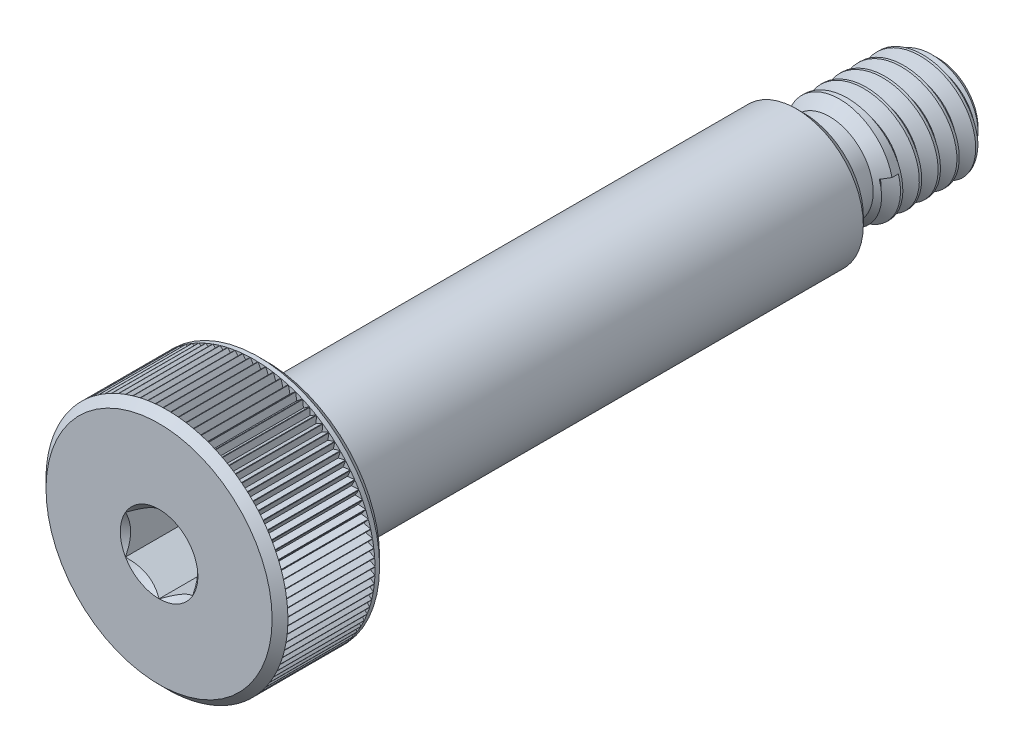
SolidWorks part; units mm, degrees
ref_plane "Front Plane" through (0, 0, 0) normal (0, 0, 1) x (1, 0, 0)
ref_plane "Top Plane" through (0, 0, 0) normal (0, 1, 0) x (1, 0, 0)
ref_plane "Right Plane" through (0, 0, 0) normal (1, 0, 0) x (0, 0, -1)
sketch "Sketch1" plane through (0, 0, 0) normal (1, 0, 0) x (0, 0, -1)
  line L0 (-14.5, 0) -> (14.5, 0) construction
  line L1 (-14.5, -4.5) -> (-14.5, 4.5) construction
  line L2 (-14.5, 4.5) -> (-10.5, 4.5) construction
  line L3 (-10.5, 4.5) -> (-10.5, 2.297) construction
  line L4 (-10.5, 2.297) -> (-9.992, 2.297) construction
  line L5 (-9.992, 2.297) -> (-9.789, 2.5) construction
  line L6 (-9.789, 2.5) -> (9.5, 2.5) construction
  line L7 (14.4563, 2.0758) -> (14.8063, 1.4696) construction
  line L8 (14.8063, 1.4696) -> (15.1563, 2.0758) construction
  line L9 (14.5, -2) -> (14.5, 2) construction
  line L10 (9.5, 2.5) -> (14.5, 2.5) construction
  line L11 (15.1563, 2.0758) -> (14.4563, 2.0758) construction
  line L12 (14.8063, 2.0758) -> (14.8063, 2) construction
  line L13 (14.8063, 1.4696) -> (14.8063, 1.5453) construction
  line L14 (14.85, 1.5453) -> (14.7625, 1.5453) construction
  line L15 (15.1125, 2) -> (14.5, 2) construction
  line L16 (14.8063, 2.0379) -> (15.1344, 2.0379) construction
  line L17 (14.8063, 2.0379) -> (14.4781, 2.0379) construction
  line L18 (-14.5, 4.2075) -> (-14.2075, 4.5) construction
  line L19 (-10.7925, 4.5) -> (-10.5, 4.2075) construction
  line L20 (14.5, 2) -> (9.5, 2) construction
  line L21 (13.975, 2) -> (14.5, 1.475) construction
  line L22 (10.825, 2) -> (10.45, 1.625) construction
  line L23 (10.45, 1.625) -> (9.6875, 1.625) construction
  line L24 (9.5, 2) -> (9.5, 1.8125) construction
  line L25 (-12.5, 1.25) -> (-12.5, -1.25) construction
  line L26 (-12.5, -1.25) -> (-14.5, -1.25) construction
  line L27 (-12.5, 1.25) -> (-14.5, 1.25) construction
  line L28 (-14.2075, 0) -> (-10.9633, 0) construction
  arc A0 (9.5, 1.8125) -> (9.6875, 1.625) centre (9.6875, 1.8125) ccw construction
  point P4 (0, 0)
  point P7 (-14.5, 0)
  point P18 (14.5, 0)
  point P25 (12.05, -2)
  point P38 (-12.5, 4.5)
  point P45 (-12.5, 0)
  point P46 (10.6375, 1.8125)
  point P48 (-9.992, 0)
  point P51 (-12.5, 0)
  point P52 (9.5, 0)
  point P53 (-7.3, 0)
  dimension "Head Diameter" = 9
  dimension "Head Height" = 4
  dimension "Thread Diameter" = 4
  dimension "Shoulder Diameter" = 5
  dimension "Thread Length" = 5
  dimension "D1" = 0.508
  dimension "D2" = 135
  dimension "D3" = 0.203
  dimension "Shoulder Length" = 20
  dimension "Thread Pitch" = 0.7
  dimension "D4" = 0.0875
  dimension "D5" = 2.45
  dimension "D6" = 0.2925
  dimension "D7" = 0.525
  dimension "D8" = 3.25
  dimension "D9" = 0.95
  dimension "Drive Size" = 2.5
  dimension "Knurling Length" = 3.2443
  dimension "D10" = 7.2
sketch "Sketch3" plane through (0, 0, 0) normal (1, 0, 0) x (0, 0, -1)
  line L0 (-14.5, 0) -> (-14.5, 4.2075)
  line L1 (-14.5, -4.5) -> (-14.5, 4.5) construction
  line L2 (-14.5, 4.2075) -> (-14.2075, 4.5)
  line L3 (-14.2075, 4.5) -> (-10.7925, 4.5)
  line L4 (-10.7925, 4.5) -> (-10.5, 4.2075)
  line L5 (-10.5, 4.2075) -> (-10.5, 2.297)
  line L6 (-10.5, 2.297) -> (-9.992, 2.297)
  line L7 (-9.992, 2.297) -> (-9.789, 2.5)
  line L8 (-9.789, 2.5) -> (9.5, 2.5)
  line L9 (9.5, 2.5) -> (9.5, 1.8125)
  line L10 (9.6875, 1.625) -> (10.45, 1.625)
  line L11 (10.45, 1.625) -> (10.825, 2)
  line L12 (10.825, 2) -> (13.975, 2)
  line L13 (13.975, 2) -> (14.5, 1.475)
  line L14 (14.5, 1.475) -> (14.5, 0)
  line L15 (14.5, 0) -> (-14.5, 0)
  arc A0 (9.5, 1.8125) -> (9.6875, 1.625) centre (9.6875, 1.8125) ccw construction
  arc A1 (9.5, 1.8125) -> (9.6875, 1.625) centre (9.6875, 1.8125) ccw
revolve "Revolve1" add sketch "Sketch3" angle 360 about L0
sketch "Sketch4" plane through (0, 0, 0) normal (0, 0, 1) x (1, 0, 0)
  line L0 (0, -4.5) -> (0, 4.5) construction
  line L1 (0, 1.4434) -> (-1.25, 0.7217)
  line L2 (-1.25, 0.7217) -> (-1.25, -0.7217)
  line L3 (-1.25, -0.7217) -> (0, -1.4434)
  line L4 (0, -1.4434) -> (1.25, -0.7217)
  line L5 (1.25, -0.7217) -> (1.25, 0.7217)
  line L6 (1.25, 0.7217) -> (0, 1.4434)
  circle A0 centre (0, 0) radius 1.25 construction
extrude "Cut-Extrude1" cut sketch "Sketch4" against normal up to vertex (-12.5 mm away) from vertex at 14.5 starting at point (0, 0, 14.5)
sketch "Sketch5" plane through (0, 0, 0) normal (0, 0, 1) x (1, 0, 0)
  line L0 (0, -4.5) -> (0, 4.5) construction
  circle A0 centre (0, 0) radius 1.4434
extrude "Cut-Extrude2" cut sketch "Sketch5" against normal up to vertex (-12.5 mm away) draft 45 from vertex at 14.5 starting at point (0, 0, 14.5)
chamfer "Chamfer1" distance 0.2925 angle 45 1 edges at (2.5, 0, -9.5)
sketch "Sketch6" plane through (0, 0, -14.5) normal (0, 0, -1) x (-1, 0, 0)
  circle A0 centre (0, 0) radius 2
curve "Helix/Spiral1" pitch 0.7 height 4.05 turns 5.7857
sketch "Sketch7" plane through (0, 0, 0) normal (1, 0, 0) x (0, 0, -1)
  line L0 (14.4781, 2.0379) -> (14.7625, 1.5453)
  line L1 (14.7625, 1.5453) -> (14.85, 1.5453)
  line L2 (14.85, 1.5453) -> (15.1344, 2.0379)
  line L3 (15.1344, 2.0379) -> (14.4781, 2.0379)
sweep "Cut-Sweep1" cut profiles "Sketch7" path "Helix/Spiral1"
sketch "Sketch8" plane through (0, 0, 0) normal (0, 0, 1) x (1, 0, 0)
  line L0 (0, 4.5) -> (0, 0) construction
  line L1 (-0.1351, 4.5) -> (0.1351, 4.5)
  line L2 (0.1351, 4.5) -> (0, 4.266)
  line L3 (0, 4.266) -> (-0.1351, 4.5)
  line L4 (-0.1351, 4.5) -> (0, 0) construction
  line L5 (0, 0) -> (0.1351, 4.5) construction
  circle A0 centre (0, 0) radius 4.266 construction
  point P8 (0, 4.5)
  dimension "D1" = 0.234
  dimension "D2" = 3.439
extrude "Cut-Extrude3" cut sketch "Sketch8" against normal up to vertex (-10.9633 mm away) from vertex at 14.2075 starting at point (0, 0, 14.2075)
pattern_circular "CirPattern1" count 99 over 360 about axis through (0, 0, 0) along (0, 0, 1) of "Cut-Extrude3"
equation "\"D4@Sketch1\"=\"Thread Pitch@Sketch1\"/8"
equation "\"D5@Sketch1\"=\"Thread Pitch@Sketch1\"*3.5"
equation "\"D6@Sketch1\"=\"Head Diameter@Sketch1\"*.0325"
equation "\"D7@Sketch1\"=\"Thread Pitch@Sketch1\"*.75"
equation "\"D1@Chamfer1\"=\"D6@Sketch1\""
equation "\"D4@Helix/Spiral1\"=\"Thread Pitch@Sketch1\""
equation "\"D3@Helix/Spiral1\" = \"Thread Length@Sketch1\" - \"D9@Sketch1\""
equation "\"D1@Sketch8\"=\"D6@Sketch1\"*.8"
equation "\"D1@CirPattern1\"=(360/\"D2@Sketch8\")-6"
equation "\"D9@Sketch1\"  = \"Thread Length@Sketch1\"*.2"
equation "\"D8@Sketch1\"=\"Thread Diameter@Sketch1\"*.65"
equation "\"D10@Sketch1\"=\"Head Diameter@Sketch1\"*.8"
